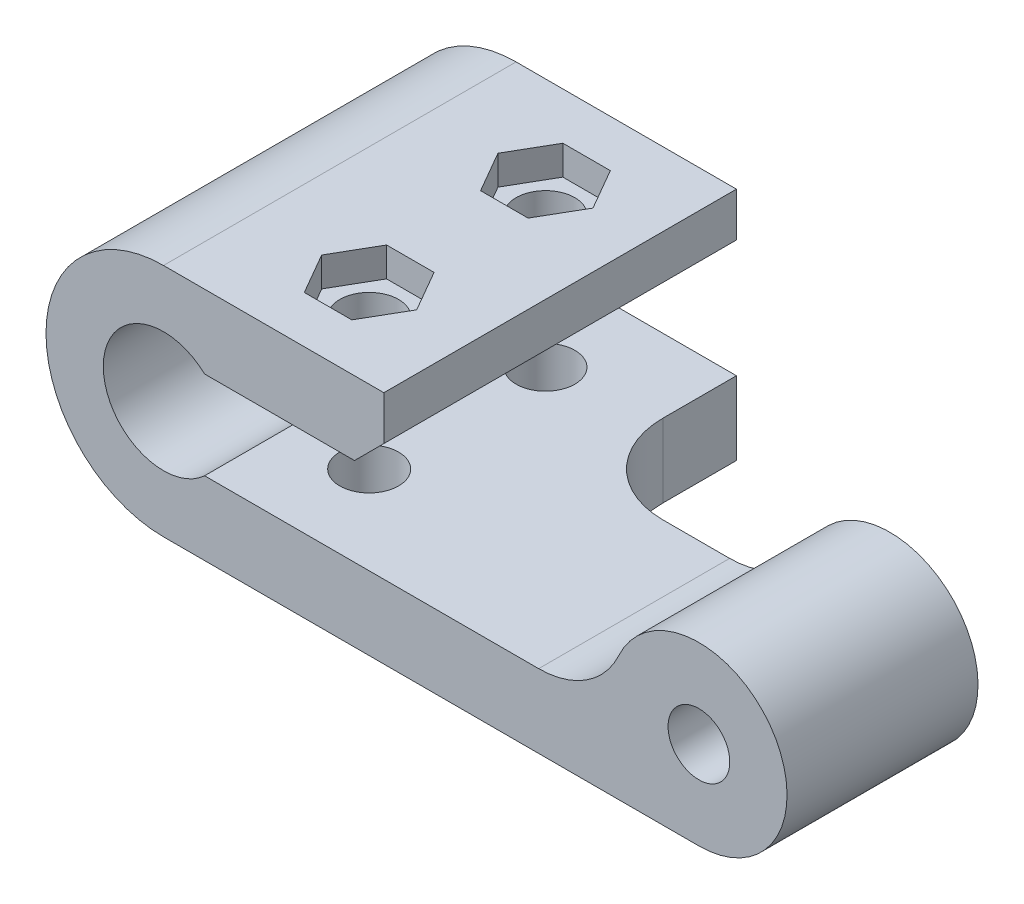
SolidWorks part; units mm, degrees
ref_plane "Front Plane" through (0, 0, 0) normal (0, 0, 1) x (1, 0, 0)
ref_plane "Top Plane" through (0, 0, 0) normal (0, 1, 0) x (1, 0, 0)
ref_plane "Right Plane" through (0, 0, 0) normal (1, 0, 0) x (0, 0, -1)
sketch "Sketch1" plane through (0, 0, 0) normal (0, 0, 1) x (1, 0, 0)
  line L0 (2.7946, 3) -> (15, 3)
  line L1 (15, 3) -> (15, 8)
  line L2 (15, 8) -> (0, 8)
  line L3 (0, -8) -> (36.4452, -8)
  line L5 (25.5365, -3) -> (2.7946, -3)
  line L6 (7, 8) -> (7, -8) construction
  line L7 (5.5, 8) -> (5.5, -8) construction
  line L8 (8.5, -8) -> (8.5, 8) construction
  line L10 (32.9452, 0.0207) -> (32.9452, -4.0207) construction
  line L11 (32.9452, -4.0207) -> (36.4452, -6.0415) construction
  line L12 (36.4452, -6.0415) -> (39.9452, -4.0207) construction
  line L13 (39.9452, -4.0207) -> (39.9452, 0.0207) construction
  line L14 (39.9452, 0.0207) -> (36.4452, 2.0415) construction
  line L15 (36.4452, 2.0415) -> (32.9452, 0.0207) construction
  arc A0 (2.7946, 3) -> (2.7946, -3) centre (0, 0) ccw
  arc A1 (0, 8) -> (0, -8) centre (0, 0) ccw
  arc A2 (36.4452, -8) -> (30.9908, 0.5) centre (36.4452, -2) ccw
  circle A3 centre (36.4452, -2) radius 2.1
  circle A4 centre (36.4452, -2) radius 3.5 construction
  arc A5 (30.9908, 0.5) -> (25.5365, -3) centre (25.5365, 3) cw
  dimension "D2" = 8.2
  dimension "D3" = 16
  dimension "D9" = 4.2
  dimension "D10" = 12
  dimension "D12" = 7
  dimension "D13" = 6
  dimension "D1" = 15
  dimension "D4" = 36.5
  dimension "D5" = 6
  dimension "D6" = 3
  dimension "D7" = 1.5
  dimension "D8" = 7
  dimension "D11" = 3
extrude "Boss-Extrude1" add sketch "Sketch1" along normal blind 24
sketch "Sketch2" plane through (0, -8, 0) normal (0, -1, 0) x (1, 0, 0)
  line L0 (15, 24) -> (15, 0) construction
  line L1 (15, 5) -> (15, 0)
  line L2 (21, 11) -> (45.8711, 11)
  line L3 (45.8711, 11) -> (45.8711, 0)
  line L4 (45.8711, 0) -> (15, 0)
  line L5 (0, 24) -> (36.4452, 24) construction
  line L6 (20, 12) -> (0, 12) construction
  line L7 (0, 24) -> (0, 0) construction
  line L8 (0, 24) -> (0, 0) construction
  circle A0 centre (8, 18) radius 2
  circle A1 centre (8, 6) radius 2
  arc A2 (21, 11) -> (15, 5) centre (21, 5) ccw
  dimension "D8" = 4
  dimension "D1" = 6
  dimension "D2" = 13
  dimension "D5" = 20
  dimension "D6" = 8
  dimension "D7" = 12
  dimension "D9" = 6
extrude "Cut-Extrude1" cut sketch "Sketch2" against normal through all
sketch "Sketch3" plane through (0, 8, 0) normal (0, 1, 0) x (-1, 0, 0)
  line L1 (-9.6166, 8.8) -> (-11.2332, 6)
  line L2 (-11.2332, 6) -> (-9.6166, 3.2)
  line L3 (-9.6166, 3.2) -> (-6.3834, 3.2)
  line L4 (-6.3834, 3.2) -> (-4.7668, 6)
  line L5 (-4.7668, 6) -> (-6.3834, 8.8)
  line L6 (-6.3834, 8.8) -> (-9.6166, 8.8)
  line L7 (-9.6166, 20.8) -> (-11.2332, 18)
  line L8 (-11.2332, 18) -> (-9.6166, 15.2)
  line L9 (-9.6166, 15.2) -> (-6.3834, 15.2)
  line L10 (-6.3834, 15.2) -> (-4.7668, 18)
  line L11 (-4.7668, 18) -> (-6.3834, 20.8)
  line L12 (-6.3834, 20.8) -> (-9.6166, 20.8)
  circle A0 centre (-8, 6) radius 2.8 construction
  circle A1 centre (-8, 18) radius 2.8 construction
  dimension "D1" = 5.6
extrude "Cut-Extrude2" cut sketch "Sketch3" against normal blind 2
sketch "Sketch4" plane through (0, 0, 11) normal (0, 0, -1) x (-1, 0, 0)
  line L1 (-34.4244, 1.5) -> (-38.4659, 1.5)
  line L2 (-38.4659, 1.5) -> (-40.4866, -2)
  line L3 (-40.4866, -2) -> (-38.4659, -5.5)
  line L4 (-38.4659, -5.5) -> (-34.4244, -5.5)
  line L5 (-34.4244, -5.5) -> (-32.4037, -2)
  line L6 (-32.4037, -2) -> (-34.4244, 1.5)
  circle A0 centre (-36.4452, -2) radius 3.5 construction
  dimension "D1" = 7
extrude "Cut-Extrude3" cut sketch "Sketch4" against normal blind 5
chamfer "Chamfer1" distance 2 angle 45 1 edges at (15, 3, 12)
